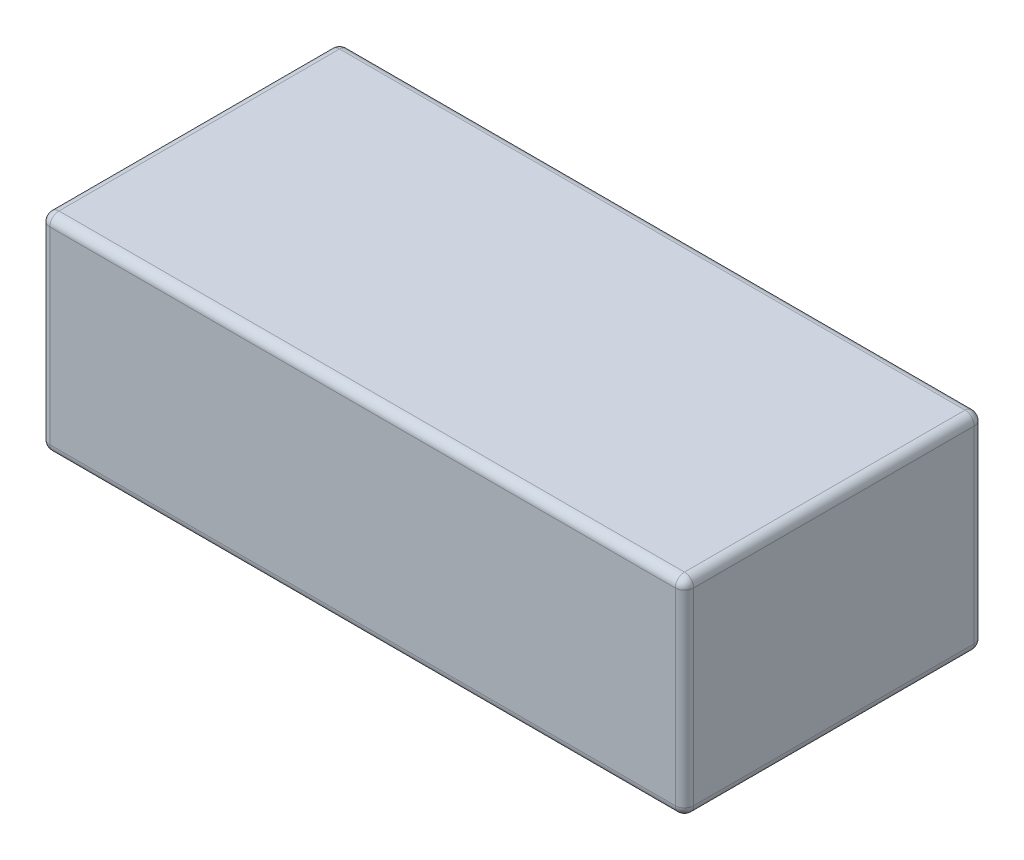
SolidWorks part; units mm, degrees
ref_plane "Piano frontale" through (0, 0, 0) normal (0, 0, 1) x (1, 0, 0)
ref_plane "Piano superiore" through (0, 0, 0) normal (0, 1, 0) x (1, 0, 0)
ref_plane "Piano destro" through (0, 0, 0) normal (1, 0, 0) x (0, 0, -1)
sketch "Schizzo1" plane through (0, 0, 0) normal (0, 0, 1) x (1, 0, 0)
  line L1 (-70, -22.5) -> (70, -22.5)
  line L2 (-70, -22.5) -> (-70, 22.5)
  line L3 (-70, 22.5) -> (70, 22.5)
  line L4 (70, -22.5) -> (70, 22.5)
  line L5 (-70, -22.5) -> (70, 22.5) construction
  line L6 (-70, 22.5) -> (70, -22.5) construction
  point P0 (0, 0)
  dimension "D1" = 140
  dimension "D2" = 45
extrude "Estrusione-Estrusione1" add sketch "Schizzo1" along normal mid plane 65
fillet "Raccordo1" radius 2 12 edges at (-70, 22.5, 0) (-70, -22.5, 0) (70, -22.5, 0) (70, 22.5, 0) (0, 22.5, -32.5) (-70, 0, -32.5) (0, -22.5, -32.5) (70, 0, -32.5) (0, -22.5, 32.5) (-70, 0, 32.5) (0, 22.5, 32.5) (70, 0, 32.5)
ref_point "Point1"
